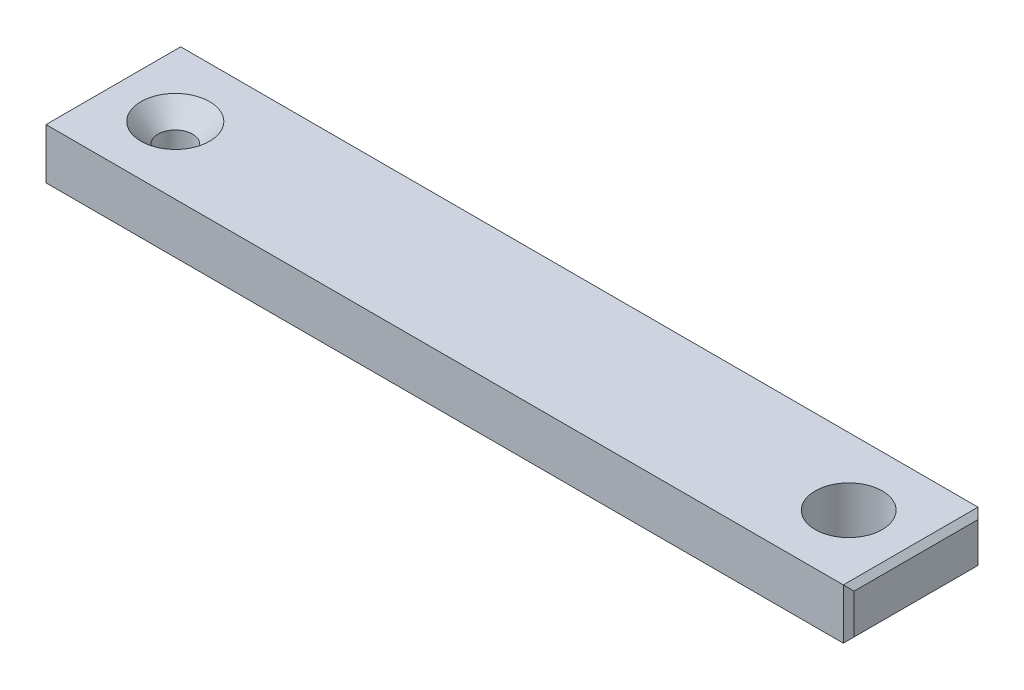
SolidWorks part; units mm, degrees
material "6061-T6 (SS)"
ref_plane "Front Plane" through (0, 0, 0) normal (0, 0, 1) x (1, 0, 0)
ref_plane "Top Plane" through (0, 0, 0) normal (0, 1, 0) x (1, 0, 0)
ref_plane "Right Plane" through (0, 0, 0) normal (1, 0, 0) x (0, 0, -1)
sketch "Sketch1" plane through (0, 0, 0) normal (0, 1, 0) x (1, 0, 0)
  line L0 (-63.5, 0) -> (0, 0) construction
  line L1 (-63.5, 6.35) -> (0, 6.35)
  line L2 (-63.5, -6.35) -> (0, -6.35)
  line L4 (-69.85, 6.35) -> (6.35, 6.35)
  line L5 (-69.85, 6.35) -> (-69.85, -6.35)
  line L6 (-69.85, -6.35) -> (6.35, -6.35)
  line L7 (6.35, 6.35) -> (6.35, -6.35)
  arc A0 (-63.5, 6.35) -> (-63.5, -6.35) centre (-63.5, 0) ccw
  arc A1 (0, -6.35) -> (0, 6.35) centre (0, 0) ccw
  point P2 (-31.75, 0)
  point P9 (-69.85, 0)
  point P10 (6.35, 0)
  dimension "D2" = 76.2
  dimension "D1" = 12.7
extrude "Boss-Extrude2" add sketch "Sketch1" along normal blind 4.7625
sketch "Sketch2" plane through (0, 4.7625, 0) normal (0, 1, 0) x (1, 0, 0)
  line L0 (6.35, 6.35) -> (6.35, -6.35) construction
  line L5 (0, 6.35) -> (0, -6.35)
  line L6 (-69.85, -6.35) -> (6.35, -6.35) construction
  line L7 (-69.85, 6.35) -> (6.35, 6.35) construction
  circle A0 centre (0, 0) radius 3.1623
  dimension "D1" = 6.3246
  dimension "D2" = 6.35
hole_wizard "CSK for #4 Flat Head Socket Cap Screw1" positions "Sketch3" profile "Sketch4" countersink size "#4" standard "ANSI Inch" end condition through all
sketch "Sketch3" plane through (0, 4.7625, 0) normal (0, 1, 0) x (1, 0, 0)
  line L0 (-63.5, 6.35) -> (-63.5, -6.35)
  line L1 (-69.85, 6.35) -> (6.35, 6.35) construction
  line L2 (-69.85, -6.35) -> (6.35, -6.35) construction
  line L4 (-69.85, 6.35) -> (-69.85, -6.35) construction
  point P0 (-63.5, 0)
  dimension "D1" = 6.35
sketch "Sketch4" plane through (-63.5, 4.7625, 0) normal (1, 0, 0) x (0, 0, 1)
  line L0 (0, 0) -> (0, 4.7625)
  line L1 (0, 4.7625) -> (1.6319, 4.7625)
  line L2 (1.6319, 4.7625) -> (1.6319, 1.8481)
  line L3 (1.6319, 1.8481) -> (3.2385, 0)
  line L5 (3.2385, 0) -> (0, 0)
  line L6 (-1.632, 1.8481) -> (-3.2385, 0) construction
  line L11 (0, -6.35) -> (0, 107.95) construction
  dimension "Thru Hole Dia." = 3.2639
  dimension "Thru Hole Depth" = 4.7625
  dimension "Near C'Sink Dia." = 6.477
  dimension "Near C'Sink Angle" = 82
extrude "Cut-Extrude1" cut sketch "Sketch2" against normal through all contours L5 A0 | L5 A0
chamfer "Chamfer1" distance 0.508 angle 45 8 edges at (-69.85, 2.3813, -6.35) (-69.85, 4.7625, 0) (-69.85, 2.3813, 6.35) (-69.85, 0, 0) (6.35, 2.3813, 6.35) (6.35, 4.7625, 0) (6.35, 2.3813, -6.35) (6.35, 0, 0)
